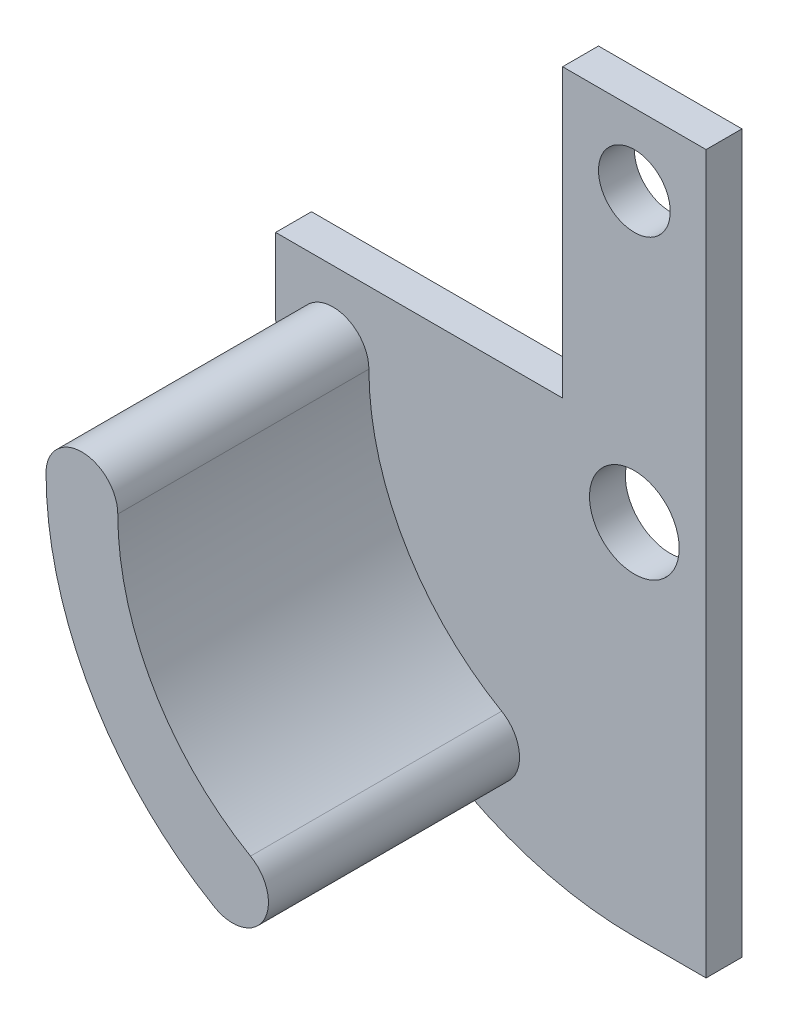
SolidWorks part; units mm, degrees
ref_plane "Front Plane" through (0, 0, 0) normal (0, 0, 1) x (1, 0, 0)
ref_plane "Top Plane" through (0, 0, 0) normal (0, 1, 0) x (1, 0, 0)
ref_plane "Right Plane" through (0, 0, 0) normal (1, 0, 0) x (0, 0, -1)
sketch "Sketch1" plane through (0, 0, 0) normal (0, 0, 1) x (1, 0, 0)
  line L0 (-31.75, 0) -> (-31.75, 6.35)
  line L1 (0, -31.75) -> (6.35, -31.75)
  line L2 (6.35, -31.75) -> (6.35, 6.35)
  line L3 (-6.35, 6.35) -> (-31.75, 6.35)
  line L4 (6.35, 6.35) -> (6.35, 31.75)
  line L5 (6.35, 31.75) -> (-6.35, 31.75)
  line L6 (-6.35, 31.75) -> (-6.35, 6.35)
  arc A0 (0, -31.75) -> (-31.75, 0) centre (0, 0) cw
  circle A1 centre (-26.67, 0) radius 3.175 construction
  circle A2 centre (0, -26.67) radius 3.175 construction
  circle A3 centre (0, 0) radius 3.9688 construction
  circle A4 centre (0, 25.4) radius 3.175 construction
  dimension "D1" = 31.75
  dimension "D2" = 6.35
  dimension "D3" = 6.35
  dimension "D4" = 7.9375
  dimension "D7" = 26.67
  dimension "D11" = 6.35
  dimension "D5" = 6.35
  dimension "D6" = 6.35
  dimension "D8" = 26.67
  dimension "D9" = 6.35
  dimension "D10" = 31.75
  dimension "D12" = 25.4
extrude "Boss-Extrude1" add sketch "Sketch1" along normal blind 3.175
sketch "Sketch4" plane through (0, 0, 3.175) normal (0, 0, 1) x (1, 0, 0)
  circle A0 centre (0, 0) radius 3.9688
  circle A1 centre (0, 25.4) radius 3.175
  dimension "D1" = 7.9375
  dimension "D2" = 6.35
  dimension "D3" = 25.4
extrude "Cut-Extrude1" cut sketch "Sketch4" against normal through all
sketch "Sketch6" plane through (0, 0, 3.175) normal (0, 0, 1) x (1, 0, 0)
  arc A0 (-29.845, 0) -> (-23.495, 0) centre (-26.67, 0) cw
  arc A1 (-11.7475, -20.3473) -> (-14.9225, -25.8465) centre (-13.335, -23.0969) cw
  arc A2 (-11.7475, -20.3473) -> (-23.495, 0) centre (0, 0) cw
  arc A3 (-14.9225, -25.8465) -> (-29.845, 0) centre (0, 0) cw
  point P8 (-29.7468, 0.5285)
  point P9 (0, 0)
  point P10 (0, 0)
  point P11 (0, 0)
  point P12 (0, 0)
  point P13 (0, 0)
  point P14 (0, 0)
  point P15 (-23.495, 0.6212)
  point P16 (0, 0)
  point P17 (0, 0)
  dimension "D1" = 60
  dimension "D2" = 3.175
  dimension "D3" = 26.67
  dimension "D4" = 26.67
extrude "Boss-Extrude3" add sketch "Sketch6" along normal blind 22.225
